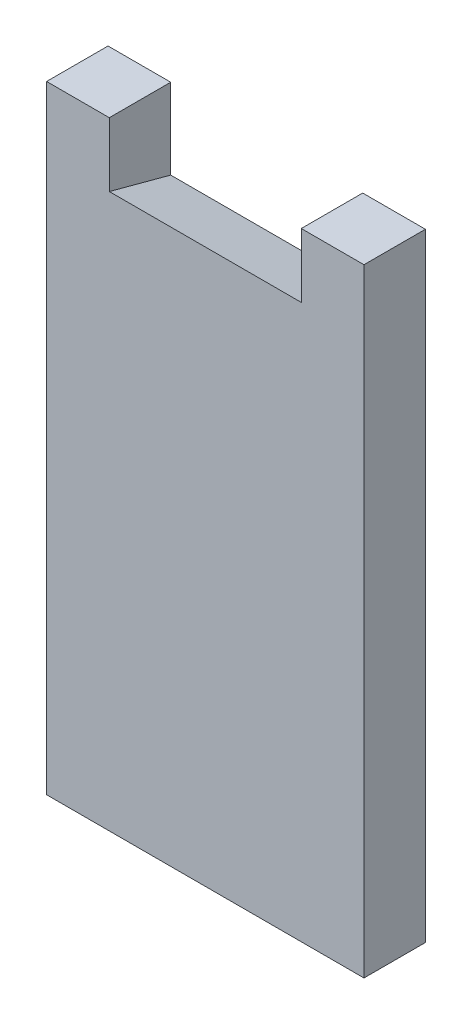
SolidWorks part; units mm, degrees
ref_plane "前视基准面" through (0, 0, 0) normal (0, 0, 1) x (1, 0, 0)
ref_plane "上视基准面" through (0, 0, 0) normal (0, 1, 0) x (1, 0, 0)
ref_plane "右视基准面" through (0, 0, 0) normal (1, 0, 0) x (0, 0, -1)
sketch "草图1" plane through (0, 0, 0) normal (0, 0, 1) x (1, 0, 0)
  line L1 (0, 0) -> (49.6, 0)
  line L2 (0, 0) -> (0, -96.54)
  line L3 (0, -96.54) -> (49.6, -96.54)
  line L4 (49.6, 0) -> (49.6, -96.54)
  line L5 (9.8, 0) -> (39.8, 0)
  line L6 (9.8, 0) -> (9.8, -10)
  line L7 (9.8, -10) -> (39.8, -10)
  line L8 (39.8, 0) -> (39.8, -10)
  point P9 (24.8, 0)
  dimension "D1" = 10
  dimension "D2" = 49.6
  dimension "D3" = 30
  dimension "D4" = 86.54
extrude "凸台-拉伸1" add sketch "草图1" along normal blind 9.6 contours L1 L8 L7 L6 L2 L3 L4
draft "拔模5" type of draft neutral plane draft angle 15 faces to draft 1 face at (24.8, -10, 4.8) neutral plane through (0, 0, 9.6) neutral plane normal (0, 0, 1) reverse direction yes parameters "D1"=15
